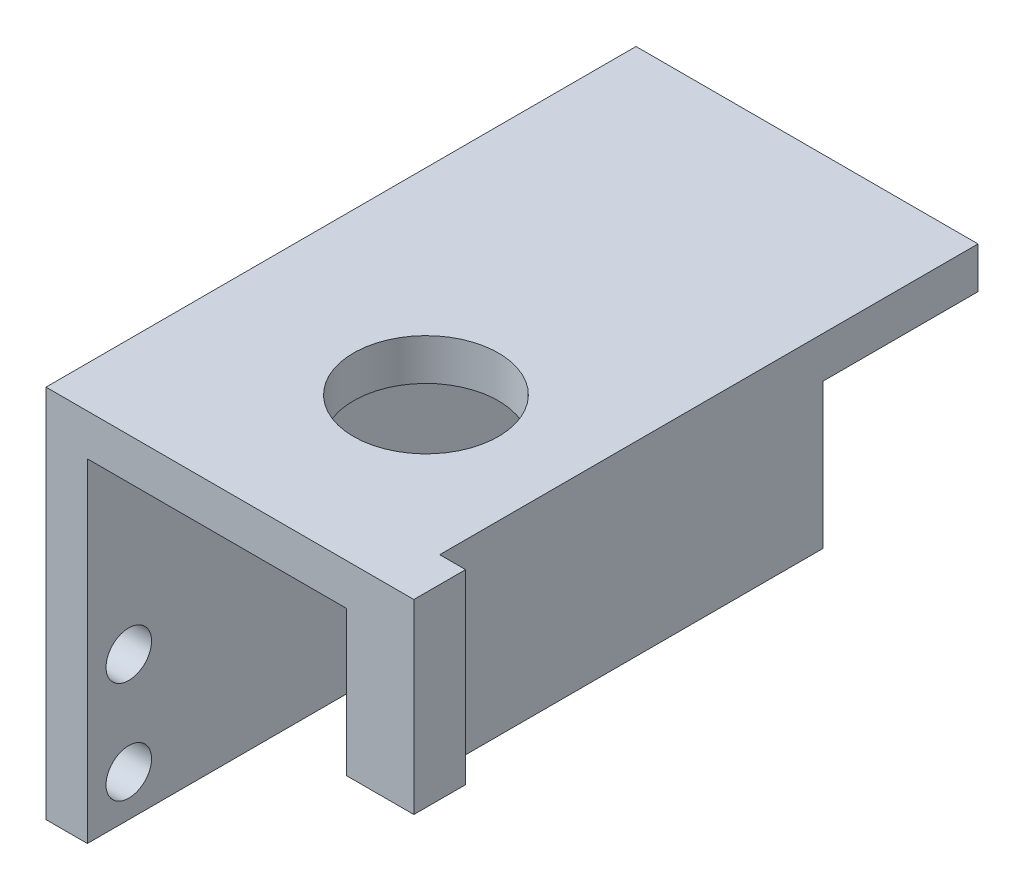
SolidWorks part; units mm, degrees
ref_plane "Front Plane" through (0, 0, 0) normal (0, 0, 1) x (1, 0, 0)
ref_plane "Top Plane" through (0, 0, 0) normal (0, 1, 0) x (1, 0, 0)
ref_plane "Right Plane" through (0, 0, 0) normal (1, 0, 0) x (0, 0, -1)
sketch "Sketch1" plane through (0, 0, 0) normal (1, 0, 0) x (0, 0, -1)
  line L1 (-28.51, 18.1) -> (28.51, 18.1)
  line L2 (-28.51, 18.1) -> (-28.51, -18.1)
  line L3 (-28.51, -18.1) -> (28.51, -18.1)
  line L4 (28.51, 18.1) -> (28.51, -18.1)
  line L5 (-28.51, 18.1) -> (28.51, -18.1) construction
  line L6 (-28.51, -18.1) -> (28.51, 18.1) construction
  circle A0 centre (-24.51, -4.25) radius 2.2
  circle A1 centre (-24.51, -14.1) radius 2.2
  circle A2 centre (24.51, -4.25) radius 2.2
  circle A3 centre (24.51, -14.1) radius 2.2
  point P0 (0, 0)
  dimension "D1" = 49.02
  dimension "D2" = 49.02
  dimension "D3" = 9.85
  dimension "D4" = 4.4
  dimension "D5" = 4.4
  dimension "D6" = 4.4
  dimension "D7" = 4.4
  dimension "D8" = 4
  dimension "D10" = 4
  dimension "D11" = 22.35
  dimension "D12" = 4
  dimension "D13" = 9.85
  dimension "D14" = 4
  dimension "D9" = 4
extrude "Boss-Extrude1" add sketch "Sketch1" along normal blind 4
sketch "Sketch2" plane through (4, 0, 0) normal (1, 0, 0) x (0, 0, -1)
  line L0 (28.51, -18.1) -> (28.51, 18.1) construction
  line L1 (-28.51, 18.1) -> (28.51, 18.1)
  line L2 (-28.51, 18.1) -> (-28.51, 14.1)
  line L3 (-28.51, 14.1) -> (28.51, 14.1)
  line L4 (28.51, 18.1) -> (28.51, 14.1)
  dimension "D1" = 4
extrude "Boss-Extrude2" add sketch "Sketch2" along normal blind 29.05
sketch "Sketch3" plane through (0, 14.1, 0) normal (0, -1, 0) x (1, 0, 0)
  line L0 (4, 28.51) -> (4, -28.51) construction
  line L1 (33.05, 28.51) -> (29.05, 28.51)
  line L2 (33.05, 28.51) -> (33.05, -13.51)
  line L3 (33.05, -13.51) -> (29.05, -13.51)
  line L4 (29.05, 28.51) -> (29.05, -13.51)
  line L5 (33.05, 28.51) -> (33.05, -28.51) construction
  line L7 (33.05, -28.51) -> (4, -28.51) construction
  line L8 (33.05, 28.51) -> (4, 28.51) construction
  dimension "D2" = 15
  dimension "D3" = 25.05
extrude "Boss-Extrude3" add sketch "Sketch3" along normal blind 14
sketch "Sketch5" plane through (0, 18.1, 0) normal (0, 1, 0) x (1, 0, 0)
  line L0 (0, 28.51) -> (0, -28.51) construction
  line L1 (33.05, -28.51) -> (0, -28.51) construction
  circle A0 centre (19, -10.79) radius 7
  dimension "D2" = 17.72
  dimension "D3" = 14
  dimension "D1" = 19
extrude "Cut-Extrude1" cut sketch "Sketch5" against normal up to surface (4 mm away) up to face at (22.0333, 14.1, -4.5033)
sketch "Sketch6" plane through (33.05, 0, 0) normal (1, 0, 0) x (0, 0, -1)
  line L0 (13.51, 0.1) -> (-28.51, 0.1) construction
  line L1 (-28.51, 18.1) -> (-23.51, 18.1)
  line L2 (-28.51, 18.1) -> (-28.51, 0.1)
  line L3 (-28.51, 0.1) -> (-23.51, 0.1)
  line L4 (-23.51, 18.1) -> (-23.51, 0.1)
  dimension "D1" = 5
extrude "Boss-Extrude4" add sketch "Sketch6" along normal blind 2.5
